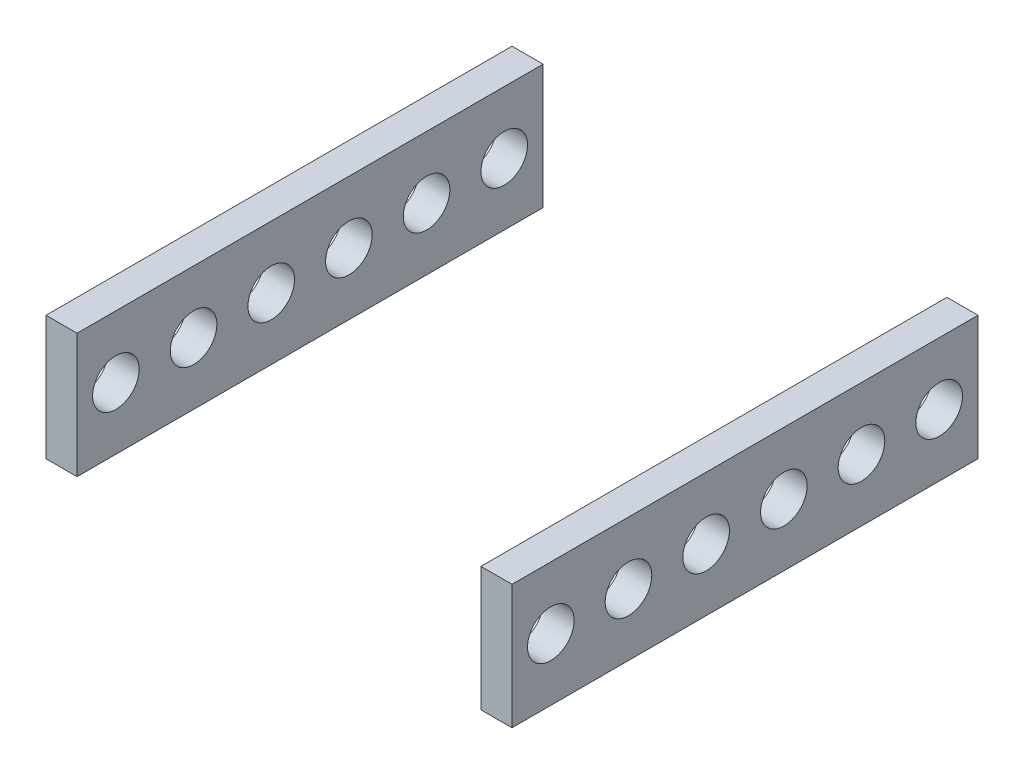
SolidWorks part; units mm, degrees
ref_plane "Front Plane" through (0, 0, 0) normal (0, 0, 1) x (1, 0, 0)
ref_plane "Top Plane" through (0, 0, 0) normal (0, 1, 0) x (1, 0, 0)
ref_plane "Right Plane" through (0, 0, 0) normal (1, 0, 0) x (0, 0, -1)
sketch "Sketch1" plane through (0, 0, 0) normal (0, 0, 1) x (1, 0, 0)
  line L0 (5.1551, -10.8738) -> (-254.8321, -8.2961)
  line L1 (5.1551, 29.1262) -> (25.1551, 29.1262)
  line L2 (5.1551, 29.1262) -> (5.1551, -50.8738)
  line L3 (5.1551, -50.8738) -> (25.1551, -50.8738)
  line L4 (25.1551, 29.1262) -> (25.1551, -50.8738)
  line L5 (-124.8385, -9.585) -> (-124.8385, 45.4307)
  line L6 (-254.8321, -50.8738) -> (-274.8321, -50.8738)
  line L7 (-274.8321, 29.1262) -> (-274.8321, -50.8738)
  line L8 (-254.8321, 29.1262) -> (-254.8321, -50.8738)
  line L9 (-254.8321, 29.1262) -> (-274.8321, 29.1262)
extrude "Boss-Extrude1" add sketch "Sketch1" along normal blind 300 contours L4 L1 L2 L3 | L8 L9 L7 L6
sketch "Sketch2" plane through (-274.8321, 0, 0) normal (-1, 0, 0) x (0, 0, 1)
  circle A0 centre (25, -10.8738) radius 15
extrude "Cut-Extrude1" cut sketch "Sketch2" against normal blind 300
sketch "Sketch3" plane through (-274.8321, 0, 0) normal (-1, 0, 0) x (0, 0, 1)
  circle A0 centre (275, -10.8738) radius 15
extrude "Cut-Extrude2" cut sketch "Sketch3" against normal blind 300
pattern_linear "LPattern1" count 6 spacing 50 along (0, 0, 1) of "Cut-Extrude1"
